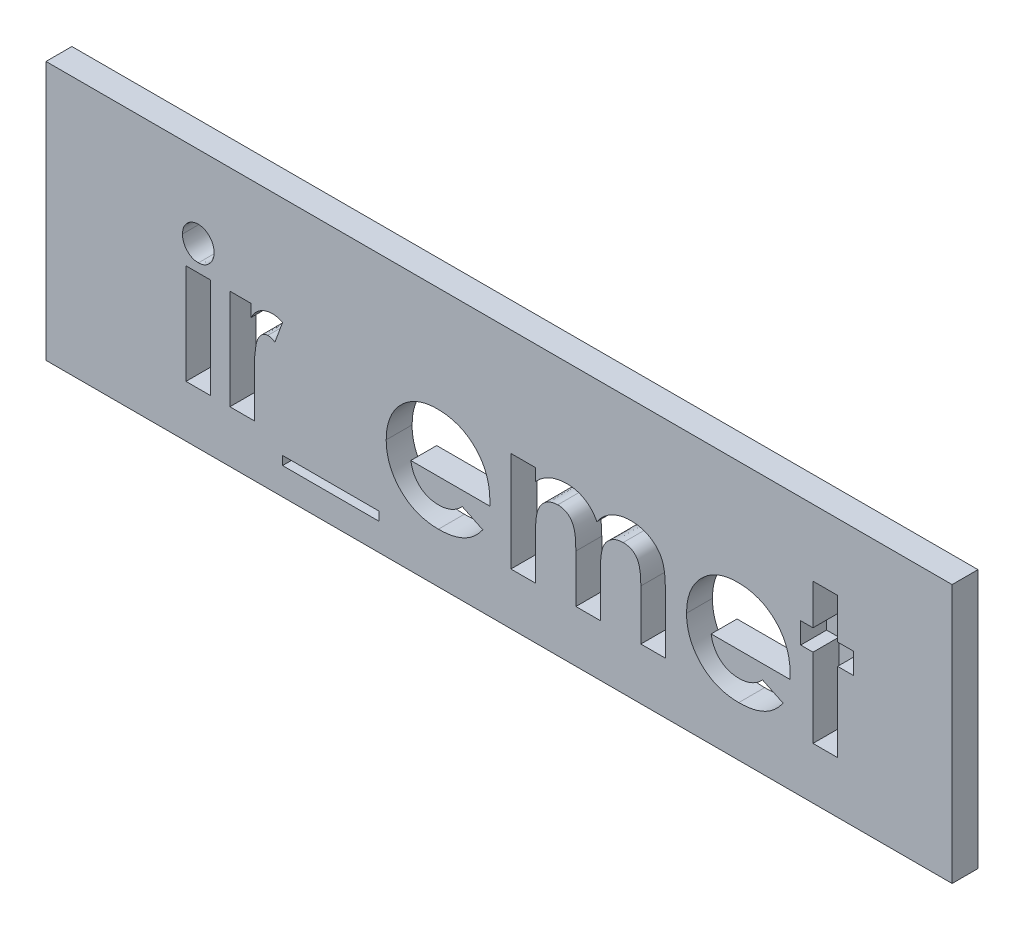
SolidWorks part; units mm, degrees
ref_plane "Plan de face" through (0, 0, 0) normal (0, 0, 1) x (1, 0, 0)
ref_plane "Plan de dessus" through (0, 0, 0) normal (0, 1, 0) x (1, 0, 0)
ref_plane "Plan de droite" through (0, 0, 0) normal (1, 0, 0) x (0, 0, -1)
sketch "Esquisse1" plane through (0, 0, 0) normal (0, 0, 1) x (1, 0, 0)
  line L1 (0, 0) -> (35, 0)
  line L2 (0, 0) -> (0, -10)
  line L3 (0, -10) -> (35, -10)
  line L4 (35, 0) -> (35, -10)
  dimension "D1" = 35
  dimension "D2" = 10
extrude "Boss.-Extru.1" add sketch "Esquisse1" along normal blind 1
sketch "Esquisse2" plane through (0, 0, 0) normal (0, 0, -1) x (-1, 0, 0)
  line L0 (-35, 0) -> (0, 0) construction
  line L1 (-35, -10) -> (-35, 0) construction
  line L2 (0, 0) -> (0, -10) construction
  circle A0 centre (-30, -5) radius 1
  circle A1 centre (-5, -5) radius 1
  dimension "D4" = 2
  dimension "D1" = 5
  dimension "D2" = 5
  dimension "D3" = 5
extrude "Boss.-Extru.2" add sketch "Esquisse2" along normal blind 3
chamfer "Chanfrein1" distance 0.5 angle 45 2 edges at (29, -5, -3) (4, -5, -3)
sketch "Esquisse3" plane through (0, 0, 1) normal (0, 0, 1) x (1, 0, 0)
  line L0 (5, -8) -> (30, -8) construction
  line L3 (0, -10) -> (35, -10) construction
  line L4 (0, 0) -> (0, -10) construction
  line L5 (35, -10) -> (35, 0) construction
  text T1 "<b>ir_emet</b>" font "Century Gothic" height in points 20
  point P12 (30, -8)
  dimension "D1" = 2
  dimension "D2" = 5
  dimension "D3" = 25
  dimension "D4" = 5
extrude "Enlèv. mat.-Extru.2" cut sketch "Esquisse3" against normal blind 1
